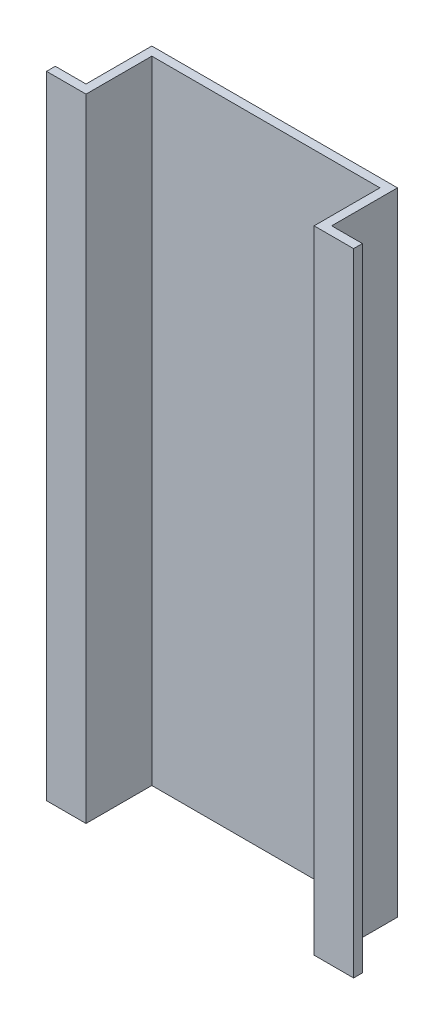
SolidWorks part; units mm, degrees
ref_plane "Front Plane" through (0, 0, 0) normal (0, 0, 1) x (1, 0, 0)
ref_plane "Top Plane" through (0, 0, 0) normal (0, 1, 0) x (1, 0, 0)
ref_plane "Right Plane" through (0, 0, 0) normal (1, 0, 0) x (0, 0, -1)
sketch "Sketch1" plane through (0, 0, 0) normal (0, 1, 0) x (1, 0, 0)
  line L0 (0, 0) -> (4, 0) construction
  line L1 (4, 0) -> (4, 7.5) construction
  line L2 (4, 7.5) -> (31, 7.5) construction
  line L3 (31, 7.5) -> (31, 0) construction
  line L4 (31, 0) -> (35, 0) construction
  line L5 (0, -0.5) -> (4.5, -0.5)
  line L6 (4.5, -0.5) -> (4.5, 7)
  line L7 (4.5, 7) -> (30.5, 7)
  line L8 (30.5, 7) -> (30.5, -0.5)
  line L9 (30.5, -0.5) -> (35, -0.5)
  line L10 (0, 0.5) -> (3.5, 0.5)
  line L11 (3.5, 0.5) -> (3.5, 8)
  line L12 (3.5, 8) -> (31.5, 8)
  line L13 (31.5, 8) -> (31.5, 0.5)
  line L14 (31.5, 0.5) -> (35, 0.5)
  line L15 (0, -0.5) -> (0, 0.5)
  line L16 (35, -0.5) -> (35, 0.5)
  dimension "D1" = 35
  dimension "D2" = 7.5
  dimension "D3" = 27
  dimension "D4" = 0.5
  dimension "D5" = 0.5
extrude "Boss-Extrude1" add sketch "Sketch1" along normal blind 72
equation "\"D1@Boss-Extrude1\"=11+(25*2)+(11*1)"
